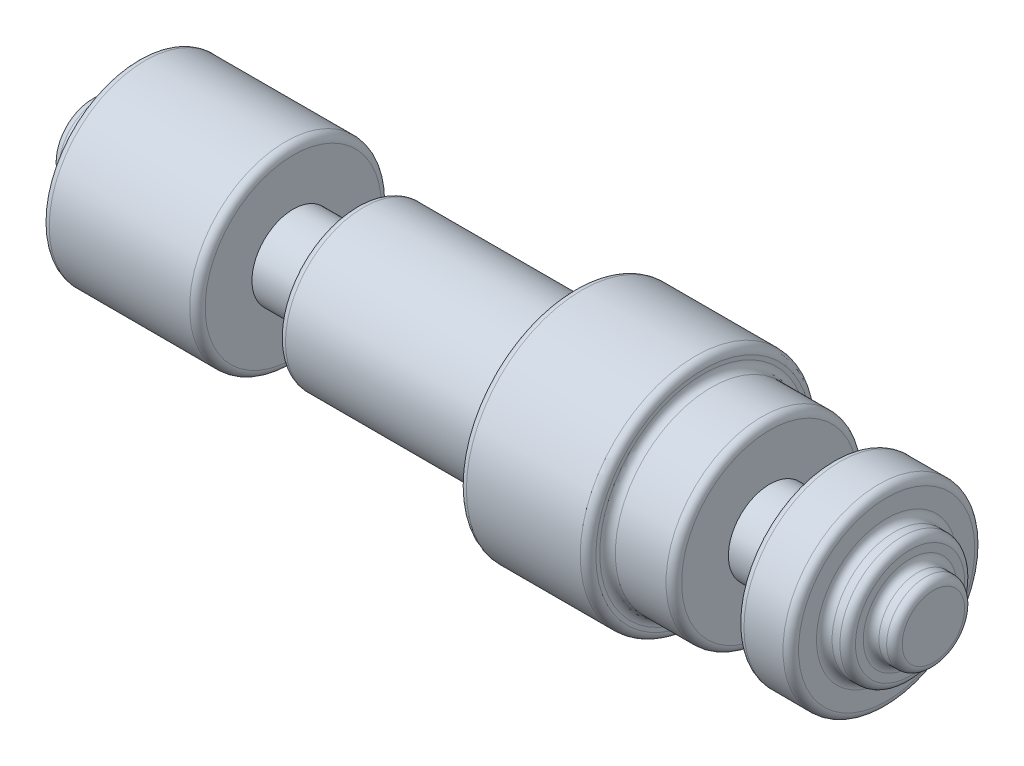
SolidWorks part; units mm, degrees
material "ABS"
ref_plane "Front Plane" through (0, 0, 0) normal (0, 0, 1) x (1, 0, 0)
ref_plane "Top Plane" through (0, 0, 0) normal (0, 1, 0) x (1, 0, 0)
ref_plane "Right Plane" through (0, 0, 0) normal (1, 0, 0) x (0, 0, -1)
sketch "Sketch1" plane through (0, 0, 0) normal (0, 0, 1) x (1, 0, 0)
  line L0 (0, 0) -> (27.4574, 0)
  line L1 (0, 0) -> (0, 1.27)
  line L2 (0, 1.27) -> (0.762, 1.27)
  line L3 (0.762, 1.27) -> (0.762, 2.032)
  line L4 (0.762, 2.032) -> (1.524, 2.032)
  line L5 (1.524, 2.032) -> (1.524, 3.1242)
  line L6 (1.524, 3.1242) -> (6.604, 3.1242)
  line L7 (6.604, 3.1242) -> (6.604, 1.3462)
  line L8 (6.604, 1.3462) -> (8.636, 1.3462)
  line L9 (8.636, 1.3462) -> (8.636, 2.54)
  line L10 (8.636, 2.54) -> (15.748, 2.54)
  line L11 (15.748, 2.54) -> (15.748, 3.7592)
  line L12 (15.748, 3.7592) -> (19.9644, 3.7592)
  line L13 (19.9644, 3.7592) -> (19.9644, 3.1242)
  line L14 (19.9644, 3.1242) -> (22.1234, 3.1242)
  line L15 (22.1234, 3.1242) -> (22.1234, 1.3462)
  line L16 (22.1234, 1.3462) -> (24.1554, 1.3462)
  line L17 (24.1554, 1.3462) -> (24.1554, 3.1242)
  line L18 (24.1554, 3.1242) -> (25.9334, 3.1242)
  line L19 (25.9334, 3.1242) -> (25.9334, 2.032)
  line L20 (25.9334, 2.032) -> (26.6954, 2.032)
  line L21 (26.6954, 2.032) -> (26.6954, 1.27)
  line L22 (26.6954, 1.27) -> (27.4574, 1.27)
  line L23 (27.4574, 1.27) -> (27.4574, 0)
  line L24 (0, 0) -> (-7.3433, 0) construction
  point P3 (13.7287, 0)
  dimension "D2" = 1.27
  dimension "D3" = 0.762
  dimension "D4" = 0.762
  dimension "D5" = 0.762
  dimension "D6" = 1.0922
  dimension "D7" = 5.08
  dimension "D8" = 1.778
  dimension "D9" = 2.032
  dimension "D10" = 7.112
  dimension "D11" = 1.2192
  dimension "D12" = 4.2164
  dimension "D13" = 0.635
  dimension "D14" = 2.159
  dimension "D15" = 1.778
  dimension "D16" = 2.032
  dimension "D17" = 1.778
  dimension "D18" = 1.27
  dimension "D19" = 0.762
  dimension "D20" = 0.762
  dimension "D21" = 0.762
  dimension "D22" = 1.0922
revolve "Revolve1" add sketch "Sketch1" angle 360 about L24
fillet "Fillet1" radius 0.254 5 edges at (1.524, 0, -3.1242) (1.524, 0, -2.032) (0.762, 0, -2.032) (0.762, 0, -1.27) (0, 0, -1.27)
fillet "Fillet2" radius 0.254 12 edges at (27.4574, 0, -1.27) (26.6954, 0, -1.27) (26.6954, 0, -2.032) (25.9334, 0, -2.032) (25.9334, 0, -3.1242) (24.1554, 0, -3.1242) (22.1234, 0, -3.1242) (19.9644, 0, -3.1242) (19.9644, 0, -3.7592) (15.748, 0, -3.7592) (8.636, 0, -2.54) (6.604, 0, -3.1242)
